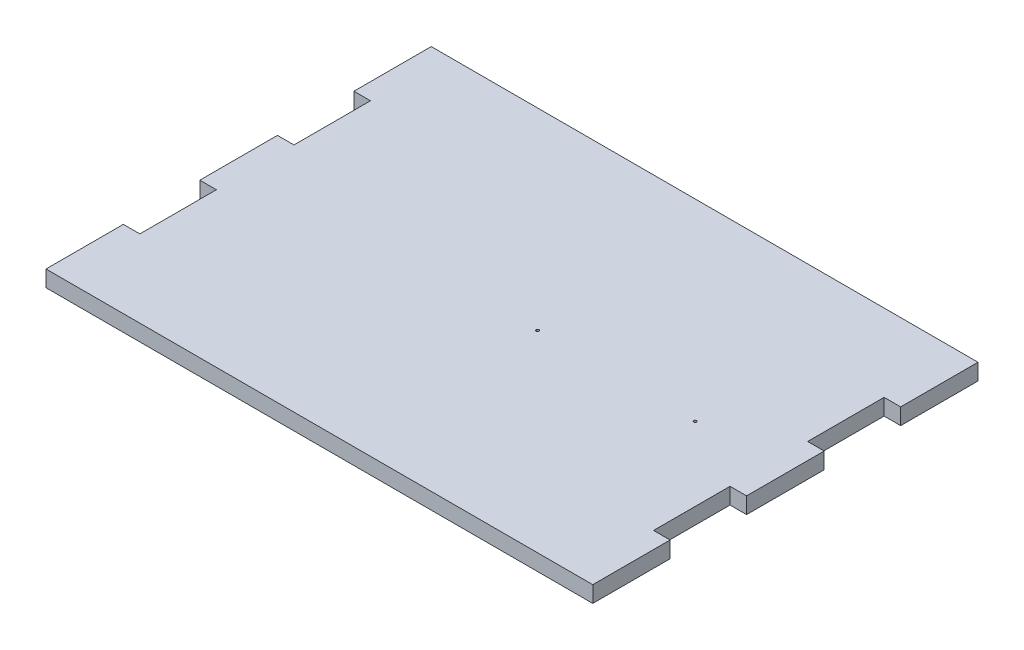
SolidWorks part; units mm, degrees
ref_plane "Front Plane" through (0, 0, 0) normal (0, 0, 1) x (1, 0, 0)
ref_plane "Top Plane" through (0, 0, 0) normal (0, 1, 0) x (1, 0, 0)
ref_plane "Right Plane" through (0, 0, 0) normal (1, 0, 0) x (0, 0, -1)
sketch "Sketch1" plane through (0, 0, 0) normal (0, 1, 0) x (1, 0, 0)
  line L0 (0, 0) -> (180, 0)
  line L1 (0, 100) -> (180, 100)
  line L2 (0, 0) -> (0, 100)
  line L4 (180, 0) -> (180, 100)
sketch "Sketch2" plane through (0, 0, 0) normal (0, 1, 0) x (1, 0, 0)
  line L1 (0, -6) -> (180, -6)
  line L2 (0, -6) -> (0, 106)
  line L3 (0, 106) -> (180, 106)
  line L4 (180, -6) -> (180, 106)
sketch "Sketch3" plane through (0, 0, 0) normal (0, 1, 0) x (1, 0, 0)
  line L1 (-6, -14) -> (186, -14)
  line L2 (-6, -14) -> (-6, 121)
  line L3 (-6, 121) -> (186, 121)
  line L4 (186, -14) -> (186, 121)
extrude "Boss-Extrude1" add sketch "Sketch3" along normal blind 5.7
ref_plane "Plane1" through (0, 5.7, 0) normal (0, 1, 0) x (1, 0, 0)
sketch "Sketch5" plane through (0, 5.7, 0) normal (0, 1, 0) x (1, 0, 0)
  line L0 (0, 0) -> (180, 0)
  line L1 (0, 100) -> (180, 100)
  line L2 (0, 0) -> (0, 100)
  line L4 (180, 0) -> (180, 100)
sketch "Sketch7" plane through (0, 5.7, 0) normal (0, 1, 0) x (1, 0, 0)
  line L1 (0, -6) -> (180, -6)
  line L2 (0, -6) -> (0, 106)
  line L3 (0, 106) -> (180, 106)
  line L4 (180, -6) -> (180, 106)
sketch "Sketch9" plane through (0, 0, 0) normal (0, 1, 0) x (1, 0, 0)
sketch "Sketch11" plane through (0, 0, 0) normal (0, 1, 0) x (1, 0, 0)
  line L1 (99, 53.5) -> (154.2, 53.5) construction
  circle A0 centre (99, 53.5) radius 0.5
  circle A1 centre (154.2, 53.5) radius 0.5
  point P0 (-6, 53.5)
extrude "Cut-Extrude2" cut sketch "Sketch11" along normal blind 33
sketch "Sketch12" plane through (0, 0, 0) normal (0, 1, 0) x (1, 0, 0)
  line L0 (-5.8, 121) -> (-5.8, 93.9)
  line L2 (-5.8, 93.9) -> (0, 93.9)
  line L4 (0, 93.9) -> (0, 67.1)
  line L5 (0, 67.1) -> (-5.8, 67.1)
  line L6 (-5.8, 67.1) -> (-5.8, 39.9)
  line L7 (-5.8, 39.9) -> (0, 39.9)
  line L8 (0, 39.9) -> (0, 13.1)
  line L9 (0, 13.1) -> (-5.8, 13.1)
  line L10 (-5.8, 13.1) -> (-5.8, -14)
  line L11 (-5.8, -14) -> (-9.8, -14)
  line L12 (-9.8, -14) -> (-9.8, 121)
  line L13 (-9.8, 121) -> (-5.8, 121)
  line L14 (90, 131) -> (90, -20) construction
  line L15 (189.8, 121) -> (185.8, 121)
  line L16 (189.8, -14) -> (189.8, 121)
  line L17 (185.8, -14) -> (189.8, -14)
  line L18 (185.8, 13.1) -> (185.8, -14)
  line L19 (180, 13.1) -> (185.8, 13.1)
  line L20 (180, 39.9) -> (180, 13.1)
  line L21 (185.8, 39.9) -> (180, 39.9)
  line L22 (185.8, 67.1) -> (185.8, 39.9)
  line L23 (180, 67.1) -> (185.8, 67.1)
  line L24 (180, 93.9) -> (180, 67.1)
  line L25 (185.8, 93.9) -> (180, 93.9)
  line L26 (185.8, 121) -> (185.8, 93.9)
extrude "Cut-Extrude3" cut sketch "Sketch12" along normal blind 22
